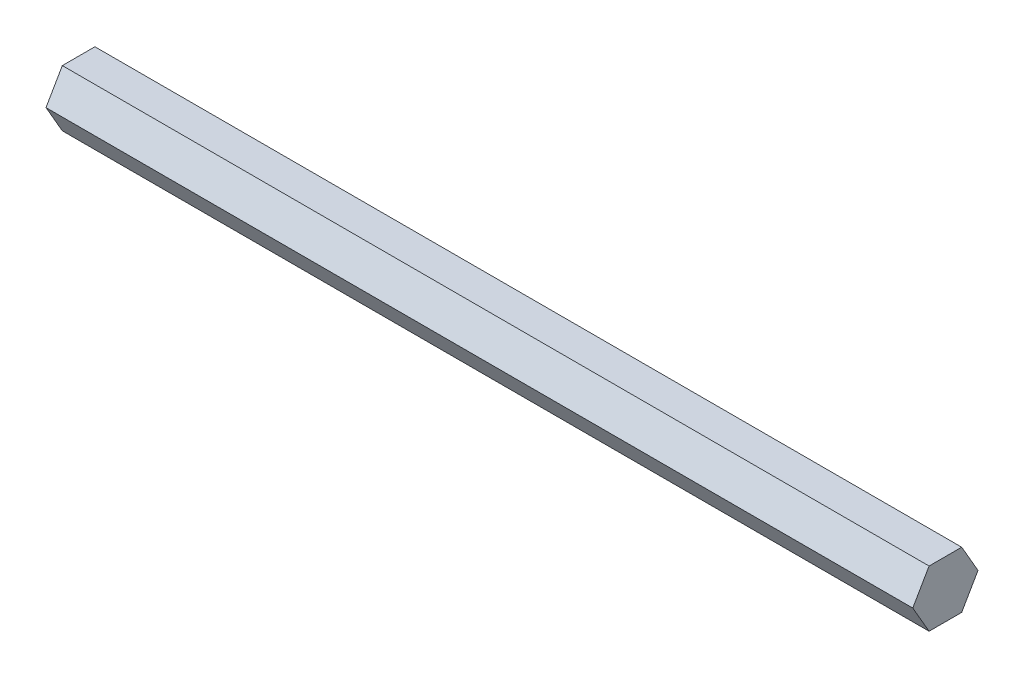
SolidWorks part; units mm, degrees
ref_plane "Front Plane" through (0, 0, 0) normal (0, 0, 1) x (1, 0, 0)
ref_plane "Top Plane" through (0, 0, 0) normal (0, 1, 0) x (1, 0, 0)
ref_plane "Right Plane" through (0, 0, 0) normal (1, 0, 0) x (0, 0, -1)
sketch "Sketch1" plane through (0, 0, 0) normal (1, 0, 0) x (0, 0, -1)
  line L1 (7.3323, 0) -> (3.6662, 6.35)
  line L2 (3.6662, 6.35) -> (-3.6662, 6.35)
  line L3 (-3.6662, 6.35) -> (-7.3323, 0)
  line L4 (-7.3323, 0) -> (-3.6662, -6.35)
  line L5 (-3.6662, -6.35) -> (3.6662, -6.35)
  line L6 (3.6662, -6.35) -> (7.3323, 0)
  circle A0 centre (0, 0) radius 6.35 construction
  dimension "D1" = 12.7
extrude "Boss-Extrude1" add sketch "Sketch1" along normal blind 194.85
